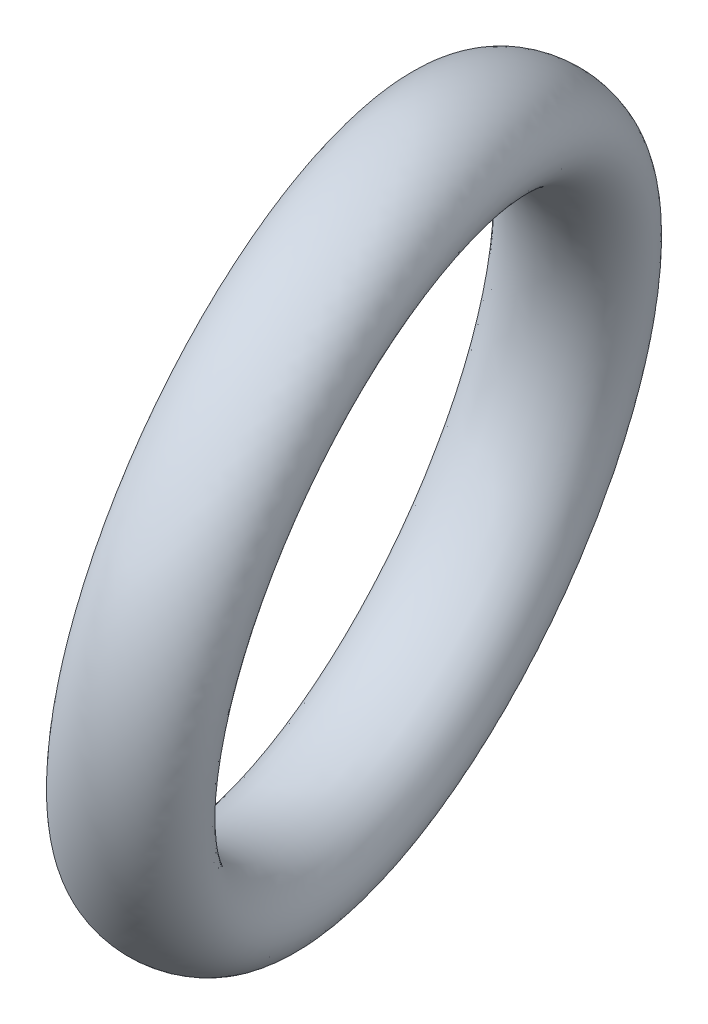
SolidWorks part; units mm, degrees
ref_plane "Front Plane" through (0, 0, 0) normal (0, 0, 1) x (1, 0, 0)
ref_plane "Top Plane" through (0, 0, 0) normal (0, 1, 0) x (1, 0, 0)
ref_plane "Right Plane" through (0, 0, 0) normal (1, 0, 0) x (0, 0, -1)
sketch "Sketch1" plane through (0, 0, 0) normal (1, 0, 0) x (0, 0, -1)
  line L0 (0, 0) -> (254, 439.9409) construction
  line L1 (0, 0) -> (0, 60.7436) construction
  line L2 (0, 0) -> (50.8, 0) construction
  line L3 (50.8, 0) -> (50.8, 263.525) construction
  line L4 (50.8, 263.525) -> (126.8097, 219.6408) construction
  circle A0 centre (50.8, 263.525) radius 263.525
  dimension "D3" = 527.05
  dimension "D1" = 508
  dimension "D2" = 30
  dimension "D4" = 50.8
  dimension "D5" = 87.7684
sketch "Sketch2" plane through (0, 0, 0) normal (0, 1, 0) x (1, 0, 0)
  line L0 (-22.2653, 83.0954) -> (0, 0) construction
  line L1 (0, 0) -> (262.9601, -981.3806) construction
  line L2 (0, 0) -> (0, 254) construction
  point P4 (-55.4206, 141.2482)
  point P7 (-22.2653, 83.0954)
  point P8 (0, 0)
  dimension "D1" = 1016
  dimension "D2" = 15
ref_plane "Plane1" through (0, 0, 0) normal (0.9553, -0.1478, -0.256) x (-0.253, 0.0391, -0.9667)
sketch "Sketch4" plane through (0, 0, 0) normal (0.9553, -0.1478, -0.256) x (-0.253, 0.0391, -0.9667)
  line L1 (247, 570.8078) -> (59.4203, 260.4271) construction
  line L2 (0, 0) -> (262.7542, 434.7692) construction
  circle A0 centre (59.4203, 260.4271) radius 263.525
  point P2 (0, 0)
  point P6 (167.2025, 261.5589)
  point P7 (133.4312, 274.9509)
  point P9 (0, 0)
  point P10 (0, 0)
  point P11 (59.4203, 260.4271)
  point P13 (59.4203, 260.4271)
  dimension "D1" = 527.05
ref_plane "Plane3" through (24.7832, 259.691, -57.4406) normal (0, -0.866, 0.5) x (-1, 0, 0)
sketch "Sketch6" plane through (24.7832, 259.691, -57.4406) normal (0, -0.866, 0.5) x (-1, 0, 0)
  line L0 (77.8919, 251.7504) -> (-77.8919, -251.7504) construction
  line L1 (77.8919, 251.7504) -> (-77.8919, -251.7504) construction
  line L2 (0, 0) -> (197.111, -60.9864) construction
  ellipse E0 centre (67.5467, 218.3143) end of major axis (22.169, 232.3542) minor radius 35
  ellipse E1 centre (67.5467, -218.3143) end of major axis (22.169, -232.3542) minor radius 35 construction
  dimension "D1" = 95
  dimension "D2" = 70
ref_plane "Plane4" through (0, 0, -57.4406) normal (0, 0, 1) x (1, 0, 0)
revolve "Revolve1" add sketch "Sketch6" angle 360 about L2
sketch "Sketch8" plane through (0, 0, -57.4406) normal (0, 0, 1) x (1, 0, 0)
  line L2 (-134.3553, 0) -> (355.2062, 0) construction
  line L10 (189.8207, 0) -> (-189.8207, 0) construction
  spline S0 degree 3 poles (38.5657, 27.377) (38.2434, 25.2939) (37.9153, 23.9442) (37.0485, 21.317) (36.5098, 20.0396) (35.5483, 18.1763) (35.2019, 17.564) (34.4707, 16.3761) (34.0847, 15.7978) (32.8691, 14.1074) (31.9819, 13.0395) (30.5457, 11.5186) (30.0476, 11.0237) (29.0274, 10.0696) (28.5053, 9.6102) (26.9053, 8.2807) (25.794, 7.4594) (23.4921, 5.9327) (22.3013, 5.2274) (19.8462, 3.9243) (18.5779, 3.3253) (14.7407, 1.7099) (12.1185, 0.86) (8.1038, -0.1266) (6.7518, -0.4069) (4.7042, -0.7576) (4.0183, -0.8628) (2.6401, -1.0501) (1.9471, -1.1323) (-1.5118, -1.484) (-4.2751, -1.5798) (-9.7946, -1.4301) (-12.5508, -1.1843) (-16.6796, -0.5583) (-18.0471, -0.3076) (-20.7501, 0.2741) (-22.0881, 0.6054) (-26.061, 1.7204) (-28.6557, 2.6243) (-32.4612, 4.237) (-33.7152, 4.8175) (-36.1923, 6.0706) (-37.4183, 6.7453) (-40.9905, 8.8857) (-43.2492, 10.4739) (-46.4278, 13.1311) (-47.4523, 14.063) (-48.9301, 15.538) (-49.414, 16.0439) (-50.3539, 17.0757) (-50.8097, 17.6012) (-52.1334, 19.2081) (-52.9578, 20.3193) (-54.4793, 22.6293) (-55.1764, 23.8281) (-56.1131, 25.7013) (-56.4075, 26.3396) (-56.9494, 27.6251) (-57.1981, 28.2742) (-57.8747, 30.241) (-58.2337, 31.5784) (-58.6205, 33.6276) (-58.7241, 34.3179) (-58.8769, 35.7139) (-58.9252, 36.4108) (-58.9856, 38.4928) (-58.9138, 39.8717) (-58.6355, 41.926) (-58.5142, 42.6084) (-58.2131, 43.9684) (-58.0322, 44.6494) (-57.4086, 46.6545) (-56.887, 47.9414) (-55.9572, 49.8027) (-55.6226, 50.4115) (-54.9052, 51.6065) (-54.5209, 52.1947) (-53.3075, 53.9103) (-52.4226, 54.9843) (-50.5188, 57.0087) (-49.4997, 57.9592) (-47.3381, 59.7459) (-46.2153, 60.5659) (-42.739, 62.8366) (-40.2782, 64.0999) (-37.0533, 65.4183) (-36.3996, 65.6692) (-35.0885, 66.1413) (-34.4301, 66.3631) (-32.4471, 66.9881) (-31.1144, 67.3509) (-27.0874, 68.2923) (-24.3642, 68.7251) (-20.917, 69.0469) (-20.2254, 69.1002) (-18.8378, 69.1849) (-18.1407, 69.2163) (-16.0532, 69.2778) (-14.666, 69.2752) (-10.5169, 69.1431) (-7.7675, 68.8899) (-3.6679, 68.2696) (-2.3055, 68.0225) (0.411, 67.4461) (1.7686, 67.1156) (5.7807, 66.0099) (8.3869, 65.1196) (13.4574, 63.0214) (15.9218, 61.814) (19.4973, 59.7318) (20.6688, 58.9924) (22.3921, 57.8072) (22.9614, 57.3989) (24.0777, 56.5632) (24.6259, 56.1349) (27.3157, 53.9399) (29.3058, 52.0147) (31.9913, 48.813) (32.8384, 47.6879) (34.3795, 45.3705) (35.0785, 44.1732) (36.3184, 41.6937) (36.8596, 40.4115) (37.7602, 37.7495) (38.1092, 36.3997) (38.5935, 33.6678) (38.7294, 32.2847) (38.7599, 30.1818) (38.7409, 29.4767) (38.6438, 28.0761) (38.5657, 27.377) (38.2434, 25.2939) (37.9153, 23.9442) knots -0.007812 -0.007812 0 0 0.015625 0.015625 0.03125 0.03125 0.039062 0.039062 0.046875 0.046875 0.0625 0.0625 0.070312 0.070312 0.078125 0.078125 0.09375 0.09375 0.109375 0.109375 0.125 0.125 0.15625 0.15625 0.171875 0.171875 0.179687 0.179687 0.1875 0.1875 0.21875 0.21875 0.25 0.25 0.265625 0.265625 0.28125 0.28125 0.3125 0.3125 0.328125 0.328125 0.34375 0.34375 0.375 0.375 0.390625 0.390625 0.398437 0.398437 0.40625 0.40625 0.421875 0.421875 0.4375 0.4375 0.445312 0.445312 0.453125 0.453125 0.46875 0.46875 0.476562 0.476562 0.484375 0.484375 0.5 0.5 0.507812 0.507812 0.515625 0.515625 0.53125 0.53125 0.539062 0.539062 0.546875 0.546875 0.5625 0.5625 0.578125 0.578125 0.59375 0.59375 0.625 0.625 0.632812 0.632812 0.640625 0.640625 0.65625 0.65625 0.6875 0.6875 0.695312 0.695312 0.703125 0.703125 0.71875 0.71875 0.75 0.75 0.765625 0.765625 0.78125 0.78125 0.8125 0.8125 0.84375 0.84375 0.859375 0.859375 0.867187 0.867187 0.875 0.875 0.90625 0.90625 0.921875 0.921875 0.9375 0.9375 0.953125 0.953125 0.96875 0.96875 0.984375 0.984375 0.992188 0.992188 1 1 1.015625 1.015625 1.03125 only from (38.4583, 26.6826) to (38.4583, 26.6826)
  spline S1 degree 3 poles (108.3345, 478.3699) (108.0121, 476.2854) (107.6835, 474.9346) (106.8127, 472.3061) (106.2703, 471.0285) (105.2989, 469.166) (104.9491, 468.5556) (104.2104, 467.3722) (103.8201, 466.7966) (102.5898, 465.1157) (101.6907, 464.0559) (100.2331, 462.5503) (99.7276, 462.0613) (98.6945, 461.1223) (98.1657, 460.6708) (96.5451, 459.3667) (95.4193, 458.564) (93.087, 457.0773) (91.8805, 456.3934) (90.0149, 455.4497) (89.3823, 455.1482) (88.1104, 454.577) (87.4703, 454.3067) (84.2495, 453.0264) (81.6097, 452.2286) (77.5707, 451.3165) (76.211, 451.0605) (73.4661, 450.6399) (72.0772, 450.4754) (67.9292, 450.1194) (65.1732, 450.0613) (59.6781, 450.2701) (56.9389, 450.5373) (52.8427, 451.1807) (51.4795, 451.4358) (48.7572, 452.0298) (47.4111, 452.366) (43.4217, 453.49) (40.8252, 454.3928) (35.765, 456.5217) (33.3011, 457.7472) (30.3173, 459.513) (29.7254, 459.8779) (28.5518, 460.6328) (27.9714, 461.022) (26.2608, 462.2186) (25.157, 463.0578) (21.963, 465.7085) (19.9881, 467.6507) (16.4315, 471.9806) (14.9086, 474.2971) (13.3934, 477.4218) (13.11, 478.0583) (12.5857, 479.3565) (12.3453, 480.0173) (11.7025, 482.0078) (11.3736, 483.3552) (11.0398, 485.4091) (10.9551, 486.0992) (10.8417, 487.4909) (10.8131, 488.1958) (10.8155, 490.294) (10.9328, 491.6755) (11.3936, 494.4046) (11.7378, 495.754) (12.6546, 498.4111) (13.2154, 499.6855) (14.5221, 502.1366) (15.2682, 503.3131) (16.936, 505.5733) (17.8388, 506.6318) (19.7633, 508.6238) (20.7851, 509.5574) (22.3989, 510.873) (22.9504, 511.2973) (24.0796, 512.1185) (24.6582, 512.5159) (27.5813, 514.4152) (30.0393, 515.6774) (33.8713, 517.2582) (35.1732, 517.7323) (37.1607, 518.3686) (37.8303, 518.5685) (39.1741, 518.942) (39.8475, 519.1154) (43.2215, 519.9187) (45.9429, 520.3594) (51.425, 520.8836) (54.1858, 520.9668) (57.6606, 520.8534) (58.3578, 520.8197) (59.7464, 520.7309) (60.4385, 520.6758) (62.5084, 520.479) (63.8796, 520.3059) (67.9679, 519.6627) (70.6596, 519.0701) (74.6451, 517.9288) (75.965, 517.5061) (77.931, 516.8057) (78.5849, 516.5608) (79.8798, 516.0515) (80.5216, 515.7868) (83.7021, 514.413) (86.156, 513.154) (89.6888, 511.0038) (90.8416, 510.2432) (92.5304, 509.0308) (93.0866, 508.6147) (94.1847, 507.7573) (94.7276, 507.3152) (97.382, 505.057) (99.3296, 503.0906) (101.9397, 499.8583) (102.7578, 498.7329) (104.2724, 496.3748) (104.9554, 495.1629) (106.1621, 492.6686) (106.6858, 491.3862) (107.3377, 489.4034) (107.5328, 488.7321) (107.8742, 487.37) (108.0187, 486.6867) (108.3726, 484.6301) (108.5025, 483.2502) (108.5293, 481.1662) (108.51, 480.4692) (108.4127, 479.0702) (108.3345, 478.3699) (108.0121, 476.2854) (107.6835, 474.9346) knots -0.007813 -0.007813 0 0 0.015625 0.015625 0.03125 0.03125 0.039062 0.039062 0.046875 0.046875 0.0625 0.0625 0.070312 0.070312 0.078125 0.078125 0.09375 0.09375 0.109375 0.109375 0.117187 0.117187 0.125 0.125 0.15625 0.15625 0.171875 0.171875 0.1875 0.1875 0.21875 0.21875 0.25 0.25 0.265625 0.265625 0.28125 0.28125 0.3125 0.3125 0.34375 0.34375 0.351562 0.351562 0.359375 0.359375 0.375 0.375 0.40625 0.40625 0.4375 0.4375 0.445312 0.445312 0.453125 0.453125 0.46875 0.46875 0.476562 0.476562 0.484375 0.484375 0.5 0.5 0.515625 0.515625 0.53125 0.53125 0.546875 0.546875 0.5625 0.5625 0.578125 0.578125 0.585937 0.585937 0.59375 0.59375 0.625 0.625 0.640625 0.640625 0.648437 0.648437 0.65625 0.65625 0.6875 0.6875 0.71875 0.71875 0.726562 0.726562 0.734375 0.734375 0.75 0.75 0.78125 0.78125 0.796875 0.796875 0.804687 0.804687 0.8125 0.8125 0.84375 0.84375 0.859375 0.859375 0.867187 0.867187 0.875 0.875 0.90625 0.90625 0.921875 0.921875 0.9375 0.9375 0.953125 0.953125 0.960937 0.960937 0.96875 0.96875 0.984375 0.984375 0.992187 0.992187 1 1 1.015625 1.015625 1.03125 only from (108.227, 477.6751) to (108.227, 477.6751)
  spline S2 degree 3 poles (108.3345, 478.3699) (108.0121, 476.2854) (107.6835, 474.9346) (106.8127, 472.3061) (106.2703, 471.0285) (105.2989, 469.166) (104.9491, 468.5556) (104.2104, 467.3722) (103.8201, 466.7966) (102.5898, 465.1157) (101.6907, 464.0559) (100.2331, 462.5503) (99.7276, 462.0613) (98.6945, 461.1223) (98.1657, 460.6708) (96.5451, 459.3667) (95.4193, 458.564) (93.087, 457.0773) (91.8805, 456.3934) (90.0149, 455.4497) (89.3823, 455.1482) (88.1104, 454.577) (87.4703, 454.3067) (84.2495, 453.0264) (81.6097, 452.2286) (77.5707, 451.3165) (76.211, 451.0605) (73.4661, 450.6399) (72.0772, 450.4754) (67.9292, 450.1194) (65.1732, 450.0613) (59.6781, 450.2701) (56.9389, 450.5373) (52.8427, 451.1807) (51.4795, 451.4358) (48.7572, 452.0298) (47.4111, 452.366) (43.4217, 453.49) (40.8252, 454.3928) (35.765, 456.5217) (33.3011, 457.7472) (30.3173, 459.513) (29.7254, 459.8779) (28.5518, 460.6328) (27.9714, 461.022) (26.2608, 462.2186) (25.157, 463.0578) (21.963, 465.7085) (19.9881, 467.6507) (16.4315, 471.9806) (14.9086, 474.2971) (13.3934, 477.4218) (13.11, 478.0583) (12.5857, 479.3565) (12.3453, 480.0173) (11.7025, 482.0078) (11.3736, 483.3552) (11.0398, 485.4091) (10.9551, 486.0992) (10.8417, 487.4909) (10.8131, 488.1958) (10.8155, 490.294) (10.9328, 491.6755) (11.3936, 494.4046) (11.7378, 495.754) (12.6546, 498.4111) (13.2154, 499.6855) (14.5221, 502.1366) (15.2682, 503.3131) (16.936, 505.5733) (17.8388, 506.6318) (19.7633, 508.6238) (20.7851, 509.5574) (22.3989, 510.873) (22.9504, 511.2973) (24.0796, 512.1185) (24.6582, 512.5159) (27.5813, 514.4152) (30.0393, 515.6774) (33.8713, 517.2582) (35.1732, 517.7323) (37.1607, 518.3686) (37.8303, 518.5685) (39.1741, 518.942) (39.8475, 519.1154) (43.2215, 519.9187) (45.9429, 520.3594) (51.425, 520.8836) (54.1858, 520.9668) (57.6606, 520.8534) (58.3578, 520.8197) (59.7464, 520.7309) (60.4385, 520.6758) (62.5084, 520.479) (63.8796, 520.3059) (67.9679, 519.6627) (70.6596, 519.0701) (74.6451, 517.9288) (75.965, 517.5061) (77.931, 516.8057) (78.5849, 516.5608) (79.8798, 516.0515) (80.5216, 515.7868) (83.7021, 514.413) (86.156, 513.154) (89.6888, 511.0038) (90.8416, 510.2432) (92.5304, 509.0308) (93.0866, 508.6147) (94.1847, 507.7573) (94.7276, 507.3152) (97.382, 505.057) (99.3296, 503.0906) (101.9397, 499.8583) (102.7578, 498.7329) (104.2724, 496.3748) (104.9554, 495.1629) (106.1621, 492.6686) (106.6858, 491.3862) (107.3377, 489.4034) (107.5328, 488.7321) (107.8742, 487.37) (108.0187, 486.6867) (108.3726, 484.6301) (108.5025, 483.2502) (108.5293, 481.1662) (108.51, 480.4692) (108.4127, 479.0702) (108.3345, 478.3699) (108.0121, 476.2854) (107.6835, 474.9346) knots -0.007813 -0.007813 0 0 0.015625 0.015625 0.03125 0.03125 0.039062 0.039062 0.046875 0.046875 0.0625 0.0625 0.070312 0.070312 0.078125 0.078125 0.09375 0.09375 0.109375 0.109375 0.117187 0.117187 0.125 0.125 0.15625 0.15625 0.171875 0.171875 0.1875 0.1875 0.21875 0.21875 0.25 0.25 0.265625 0.265625 0.28125 0.28125 0.3125 0.3125 0.34375 0.34375 0.351562 0.351562 0.359375 0.359375 0.375 0.375 0.40625 0.40625 0.4375 0.4375 0.445312 0.445312 0.453125 0.453125 0.46875 0.46875 0.476562 0.476562 0.484375 0.484375 0.5 0.5 0.515625 0.515625 0.53125 0.53125 0.546875 0.546875 0.5625 0.5625 0.578125 0.578125 0.585937 0.585937 0.59375 0.59375 0.625 0.625 0.640625 0.640625 0.648437 0.648437 0.65625 0.65625 0.6875 0.6875 0.71875 0.71875 0.726562 0.726562 0.734375 0.734375 0.75 0.75 0.78125 0.78125 0.796875 0.796875 0.804687 0.804687 0.8125 0.8125 0.84375 0.84375 0.859375 0.859375 0.867187 0.867187 0.875 0.875 0.90625 0.90625 0.921875 0.921875 0.9375 0.9375 0.953125 0.953125 0.960937 0.960937 0.96875 0.96875 0.984375 0.984375 0.992187 0.992187 1 1 1.015625 1.015625 1.03125 only from (108.227, 477.6751) to (108.227, 477.6751)
  spline S3 degree 3 poles (38.5657, 27.377) (38.2434, 25.2939) (37.9153, 23.9442) (37.0485, 21.317) (36.5098, 20.0396) (35.5483, 18.1763) (35.2019, 17.564) (34.4707, 16.3761) (34.0847, 15.7978) (32.8691, 14.1074) (31.9819, 13.0395) (30.5457, 11.5186) (30.0476, 11.0237) (29.0274, 10.0696) (28.5053, 9.6102) (26.9053, 8.2807) (25.794, 7.4594) (23.4921, 5.9327) (22.3013, 5.2274) (19.8462, 3.9243) (18.5779, 3.3253) (14.7407, 1.7099) (12.1185, 0.86) (8.1038, -0.1266) (6.7518, -0.4069) (4.7042, -0.7576) (4.0183, -0.8628) (2.6401, -1.0501) (1.9471, -1.1323) (-1.5118, -1.484) (-4.2751, -1.5798) (-9.7946, -1.4301) (-12.5508, -1.1843) (-16.6796, -0.5583) (-18.0471, -0.3076) (-20.7501, 0.2741) (-22.0881, 0.6054) (-26.061, 1.7204) (-28.6557, 2.6243) (-32.4612, 4.237) (-33.7152, 4.8175) (-36.1923, 6.0706) (-37.4183, 6.7453) (-40.9905, 8.8857) (-43.2492, 10.4739) (-46.4278, 13.1311) (-47.4523, 14.063) (-48.9301, 15.538) (-49.414, 16.0439) (-50.3539, 17.0757) (-50.8097, 17.6012) (-52.1334, 19.2081) (-52.9578, 20.3193) (-54.4793, 22.6293) (-55.1764, 23.8281) (-56.1131, 25.7013) (-56.4075, 26.3396) (-56.9494, 27.6251) (-57.1981, 28.2742) (-57.8747, 30.241) (-58.2337, 31.5784) (-58.6205, 33.6276) (-58.7241, 34.3179) (-58.8769, 35.7139) (-58.9252, 36.4108) (-58.9856, 38.4928) (-58.9138, 39.8717) (-58.6355, 41.926) (-58.5142, 42.6084) (-58.2131, 43.9684) (-58.0322, 44.6494) (-57.4086, 46.6545) (-56.887, 47.9414) (-55.9572, 49.8027) (-55.6226, 50.4115) (-54.9052, 51.6065) (-54.5209, 52.1947) (-53.3075, 53.9103) (-52.4226, 54.9843) (-50.5188, 57.0087) (-49.4997, 57.9592) (-47.3381, 59.7459) (-46.2153, 60.5659) (-42.739, 62.8366) (-40.2782, 64.0999) (-37.0533, 65.4183) (-36.3996, 65.6692) (-35.0885, 66.1413) (-34.4301, 66.3631) (-32.4471, 66.9881) (-31.1144, 67.3509) (-27.0874, 68.2923) (-24.3642, 68.7251) (-20.917, 69.0469) (-20.2254, 69.1002) (-18.8378, 69.1849) (-18.1407, 69.2163) (-16.0532, 69.2778) (-14.666, 69.2752) (-10.5169, 69.1431) (-7.7675, 68.8899) (-3.6679, 68.2696) (-2.3055, 68.0225) (0.411, 67.4461) (1.7686, 67.1156) (5.7807, 66.0099) (8.3869, 65.1196) (13.4574, 63.0214) (15.9218, 61.814) (19.4973, 59.7318) (20.6688, 58.9924) (22.3921, 57.8072) (22.9614, 57.3989) (24.0777, 56.5632) (24.6259, 56.1349) (27.3157, 53.9399) (29.3058, 52.0147) (31.9913, 48.813) (32.8384, 47.6879) (34.3795, 45.3705) (35.0785, 44.1732) (36.3184, 41.6937) (36.8596, 40.4115) (37.7602, 37.7495) (38.1092, 36.3997) (38.5935, 33.6678) (38.7294, 32.2847) (38.7599, 30.1818) (38.7409, 29.4767) (38.6438, 28.0761) (38.5657, 27.377) (38.2434, 25.2939) (37.9153, 23.9442) knots -0.007812 -0.007812 0 0 0.015625 0.015625 0.03125 0.03125 0.039062 0.039062 0.046875 0.046875 0.0625 0.0625 0.070312 0.070312 0.078125 0.078125 0.09375 0.09375 0.109375 0.109375 0.125 0.125 0.15625 0.15625 0.171875 0.171875 0.179687 0.179687 0.1875 0.1875 0.21875 0.21875 0.25 0.25 0.265625 0.265625 0.28125 0.28125 0.3125 0.3125 0.328125 0.328125 0.34375 0.34375 0.375 0.375 0.390625 0.390625 0.398437 0.398437 0.40625 0.40625 0.421875 0.421875 0.4375 0.4375 0.445312 0.445312 0.453125 0.453125 0.46875 0.46875 0.476562 0.476562 0.484375 0.484375 0.5 0.5 0.507812 0.507812 0.515625 0.515625 0.53125 0.53125 0.539062 0.539062 0.546875 0.546875 0.5625 0.5625 0.578125 0.578125 0.59375 0.59375 0.625 0.625 0.632812 0.632812 0.640625 0.640625 0.65625 0.65625 0.6875 0.6875 0.695312 0.695312 0.703125 0.703125 0.71875 0.71875 0.75 0.75 0.765625 0.765625 0.78125 0.78125 0.8125 0.8125 0.84375 0.84375 0.859375 0.859375 0.867187 0.867187 0.875 0.875 0.90625 0.90625 0.921875 0.921875 0.9375 0.9375 0.953125 0.953125 0.96875 0.96875 0.984375 0.984375 0.992188 0.992188 1 1 1.015625 1.015625 1.03125 only from (38.4583, 26.6826) to (38.4583, 26.6826)
sketch "Sketch9" plane through (0, 0, 0) normal (1, 0, 0) x (0, 0, -1)
  line L0 (-50.0794, 27.7046) -> (197.8955, 27.7046)
  line L1 (0, 0) -> (254, 439.9409) construction
  line L2 (15.9952, 27.7046) -> (126.8097, 219.6408)
  line L3 (-115.2994, 359.4225) -> (230.1807, 159.9595) construction
  spline S1 degree 3 poles (239.2015, 154.581) (243.9964, 162.886) (247.7851, 171.4112) (252.2369, 184.6585) (253.516, 189.1507) (254.8733, 194.8561) (255.1327, 196.0017) (255.6275, 198.3018) (255.8631, 199.4572) (256.5317, 202.9211) (256.9274, 205.232) (257.9727, 212.169) (258.4811, 216.7995) (259.153, 226.0713) (259.3164, 230.7125) (259.3181, 240.0051) (259.1563, 244.6564) (258.6779, 251.6407) (258.4791, 253.97) (258.1224, 257.4658) (257.9938, 258.6314) (257.717, 260.9631) (257.5689, 262.1298) (256.1527, 272.5996) (254.3041, 281.7444) (249.5272, 299.7376) (246.5977, 308.5858) (242.2805, 319.4664) (241.3836, 321.6348) (239.5265, 325.9479) (238.569, 328.0865) (235.6116, 334.4495) (233.5269, 338.6213) (226.9466, 350.9341) (222.1253, 358.8729) (211.6594, 374.2392) (206.0142, 381.6663) (193.9283, 396.0266) (187.5592, 402.8738) (174.2413, 415.9699) (167.2903, 422.2177) (156.4984, 431.2136) (152.8403, 434.1498) (145.4444, 439.9037) (141.7035, 442.7234) (134.1657, 448.2879) (130.3681, 451.0319) (124.669, 455.1443) (122.7691, 456.5148) (118.9805, 459.2707) (117.0918, 460.6558) (113.3449, 463.4643) (111.4863, 464.8873) (107.8322, 467.8124) (106.0355, 469.313) (103.4375, 471.686) (102.5869, 472.4991) (100.9489, 474.1742) (100.1601, 475.0369) (98.6765, 476.8411) (97.9806, 477.7815) (97.0576, 479.2932) (96.7717, 479.8127) (96.2665, 480.8771) (96.0459, 481.4237) (95.6916, 482.5559) (95.5621, 483.1299) (95.4565, 484.0003) (95.436, 484.2922) (95.428, 484.8801) (95.4406, 485.1781) (95.5321, 486.0636) (95.6625, 486.634) (95.9573, 487.4612) (96.0721, 487.7322) (96.3341, 488.2648) (96.4803, 488.5241) (96.9525, 489.2707) (97.3145, 489.7327) (97.9136, 490.3831) (98.1235, 490.5935) (98.5559, 490.9973) (98.7781, 491.1905) (99.9147, 492.1196) (100.9039, 492.747) (102.463, 493.5789) (102.9946, 493.8367) (104.0655, 494.315) (104.6066, 494.5364) (106.2439, 495.1569) (107.3542, 495.5123) (109.6024, 496.1364) (110.7406, 496.4046) (113.0396, 496.8703) (114.196, 497.0666) (117.6604, 497.5618) (119.9736, 497.7703) (124.6056, 498.0047) (126.9243, 498.0299) (131.5664, 497.9267) (133.8898, 497.7982) (137.3779, 497.503) (138.5412, 497.3874) (140.8559, 497.1251) (142.0091, 496.9783) (147.7552, 496.1701) (152.2892, 495.2891) (161.2506, 493.1287) (165.6776, 491.8482) (174.4334, 488.9205) (178.7621, 487.2729) (184.1138, 484.9926) (185.1812, 484.5254) (187.3015, 483.573) (188.3554, 483.0874) (191.499, 481.6026) (193.5704, 480.5757) (199.7143, 477.3876) (203.7167, 475.1192) (211.5431, 470.3105) (215.3671, 467.7699) (222.8414, 462.4236) (226.4916, 459.6177) (231.8373, 455.211) (233.5976, 453.7091) (237.0748, 450.6391) (238.7944, 449.0682) (247.2306, 441.0973) (253.4898, 434.3305) (265.0814, 420.0587) (270.4134, 412.5535) (276.4969, 402.7087) (277.6844, 400.7165) (280.0005, 396.6852) (281.1244, 394.6541) (284.3898, 388.5252) (286.4278, 384.3874) (292.1351, 371.8224) (295.3996, 363.2443) (299.4979, 350.0794) (300.7305, 345.6413) (302.3772, 338.9089) (302.8924, 336.6521) (303.8547, 332.1133) (304.3021, 329.8294) (306.3543, 318.4217) (307.4206, 309.2765) (308.4564, 290.9502) (308.4255, 281.7689) (307.5672, 267.9703) (307.1455, 263.3663) (306.3092, 256.4536) (305.9967, 254.1513) (305.3084, 249.571) (304.9322, 247.2899) (302.8946, 235.9291) (300.7638, 226.9828) (295.5932, 209.3486) (292.5522, 200.661) (288.2552, 189.9425) (287.3711, 187.8058) (285.556, 183.5457) (284.6243, 181.4212) (281.7747, 175.0924) (279.7985, 170.9246) (275.7161, 162.6762) (273.61, 158.5955) (269.2859, 150.5094) (267.068, 146.5038) (262.5293, 138.5619) (260.2084, 134.6255) (255.4602, 126.8242) (253.0326, 122.9594) (245.5694, 111.4864) (240.3528, 103.9997) (229.2814, 89.4548) (223.4253, 82.3975) (214.0526, 72.2068) (210.8304, 68.8756) (205.8378, 63.986) (204.1443, 62.3715) (200.7237, 59.1995) (198.9951, 57.6403) (190.2603, 49.9797) (182.9781, 44.2833) (167.8083, 33.7791) (159.9212, 28.9706) (149.6662, 23.5417) (147.5953, 22.485) (143.4132, 20.431) (141.2996, 19.4326) (134.913, 16.5354) (130.6185, 14.745) (117.627, 9.7897) (108.822, 7.0393) (90.9255, 2.6403) (81.834, 0.9914) (70.283, -0.3527) (67.9635, -0.5855) (64.4698, -0.8798) (63.3023, -0.9687) (60.971, -1.1276) (59.8063, -1.1976) (53.9872, -1.5008) (49.3466, -1.5935) (35.4682, -1.4293) (26.2735, -0.7319) (8.0003, 1.8495) (-1.0782, 3.7329) (-12.3487, 6.8798) (-14.5896, 7.5465) (-19.0321, 8.9503) (-21.2358, 9.6879) (-27.7946, 12.0076) (-32.0974, 13.6962) (-44.7959, 19.1901) (-52.9834, 23.4198) (-64.8181, 30.675) (-68.6882, 33.2459) (-74.3727, 37.3484) (-76.2506, 38.7598) (-79.9351, 41.6457) (-81.7444, 43.1219) (-87.0713, 47.6527) (-90.4885, 50.8088) (-97.0335, 57.4134) (-100.1618, 60.8614) (-103.864, 65.3819) (-104.5939, 66.2966) (-106.0316, 68.1484) (-106.7402, 69.0865) (-108.8242, 71.9276) (-110.1571, 73.8556) (-112.6972, 77.7873) (-113.9045, 79.7909) (-116.1712, 83.8871) (-117.2314, 85.9799) (-119.162, 90.2769) (-120.0253, 92.4621) (-120.9253, 95.258) (-121.0961, 95.8205) (-121.4172, 96.9529) (-121.5678, 97.5238) (-121.9817, 99.2395) (-122.2084, 100.3877) (-122.5322, 102.6962) (-122.6303, 103.8563) (-122.6344, 105.6095) (-122.6117, 106.1961) (-122.503, 107.3752) (-122.4161, 107.97) (-122.1636, 109.1316) (-121.9982, 109.702) (-121.6726, 110.537) (-121.551, 110.8115) (-121.2839, 111.3413) (-121.1379, 111.598) (-120.8188, 112.0938) (-120.6458, 112.3328) (-120.2703, 112.7917) (-120.0663, 113.013) (-119.4179, 113.6342) (-118.9432, 113.9871) (-118.1733, 114.4329) (-117.9059, 114.568) (-117.3574, 114.8093) (-117.0791, 114.9145) (-116.2338, 115.1901) (-115.6564, 115.3207) (-114.7742, 115.4555) (-114.4765, 115.4902) (-113.8828, 115.5408) (-113.5865, 115.557) (-112.6987, 115.5818) (-112.1085, 115.5672) (-110.9306, 115.4914) (-110.343, 115.4301) (-109.1696, 115.2712) (-108.5825, 115.1733) (-106.8353, 114.8383) (-105.6894, 114.5614) (-103.4212, 113.9407) (-102.299, 113.5964) (-100.0707, 112.8624) (-98.9645, 112.4725) (-95.6629, 111.2554) (-93.4838, 110.3817) (-89.1465, 108.5744) (-86.9887, 107.6399) (-82.6826, 105.7449) (-80.5345, 104.7842) (-74.0928, 101.8944) (-69.8014, 99.9597) (-61.1889, 96.1705) (-56.8683, 94.3147) (-48.1793, 90.732) (-43.8111, 89.0047) (-30.6179, 84.0616) (-21.7038, 81.0865) (-8.1122, 77.2188) (-3.5451, 76.028) (5.6675, 73.8585) (10.2818, 72.8872) (24.1429, 70.3225) (33.4108, 69.0778) (52.0032, 67.5593) (61.3277, 67.2849) (75.3595, 67.6459) (80.0443, 67.8953) (87.0832, 68.4712) (89.4315, 68.6969) (94.1321, 69.2172) (96.4877, 69.5124) (108.2045, 71.1552) (117.4204, 73.0033) (135.5315, 77.7868) (144.427, 80.7212) (157.5119, 85.9992) (161.8303, 87.9051) (167.1705, 90.4831) (168.236, 91.0087) (170.3532, 92.0759) (171.4059, 92.6179) (174.5463, 94.2693) (176.6162, 95.4042) (182.7538, 98.9119) (186.7497, 101.3876) (194.5407, 106.6266) (198.3358, 109.3898) (205.7095, 115.2262) (209.2881, 118.2993) (214.4755, 123.1674) (216.1778, 124.8368) (219.4908, 128.2392) (221.1041, 129.9741) (225.8103, 135.2828) (228.7697, 138.9605) (232.9257, 144.6976) (234.2638, 146.6468) (236.1982, 149.6271) (237.1471, 151.1315) (238.222, 152.9117) (238.7514, 153.8081) (238.9765, 154.1936) (239.1262, 154.451) (239.2015, 154.581) (243.9964, 162.886) (247.7851, 171.4112) knots -0.000244 -0.000244 0 0 0.015625 0.015625 0.023438 0.023438 0.025391 0.025391 0.027344 0.027344 0.03125 0.03125 0.039063 0.039063 0.046875 0.046875 0.054688 0.054688 0.058594 0.058594 0.060547 0.060547 0.0625 0.0625 0.078125 0.078125 0.09375 0.09375 0.097656 0.097656 0.101563 0.101563 0.109375 0.109375 0.125 0.125 0.140625 0.140625 0.15625 0.15625 0.171875 0.171875 0.179688 0.179688 0.1875 0.1875 0.195313 0.195313 0.199219 0.199219 0.203125 0.203125 0.207031 0.207031 0.210938 0.210938 0.212891 0.212891 0.214844 0.214844 0.216797 0.216797 0.217773 0.217773 0.21875 0.21875 0.219727 0.219727 0.220215 0.220215 0.220703 0.220703 0.22168 0.22168 0.222168 0.222168 0.222656 0.222656 0.223633 0.223633 0.224121 0.224121 0.224609 0.224609 0.226563 0.226563 0.227539 0.227539 0.228516 0.228516 0.230469 0.230469 0.232422 0.232422 0.234375 0.234375 0.238281 0.238281 0.242188 0.242188 0.246094 0.246094 0.248047 0.248047 0.25 0.25 0.257813 0.257813 0.265625 0.265625 0.273437 0.273437 0.275391 0.275391 0.277344 0.277344 0.28125 0.28125 0.289062 0.289062 0.296875 0.296875 0.304687 0.304687 0.308594 0.308594 0.3125 0.3125 0.328125 0.328125 0.34375 0.34375 0.347656 0.347656 0.351562 0.351562 0.359375 0.359375 0.375 0.375 0.382812 0.382812 0.386719 0.386719 0.390625 0.390625 0.40625 0.40625 0.421875 0.421875 0.429687 0.429687 0.433594 0.433594 0.4375 0.4375 0.453125 0.453125 0.46875 0.46875 0.472656 0.472656 0.476562 0.476562 0.484375 0.484375 0.492187 0.492187 0.5 0.5 0.507812 0.507812 0.515625 0.515625 0.53125 0.53125 0.546875 0.546875 0.554687 0.554687 0.558594 0.558594 0.5625 0.5625 0.578125 0.578125 0.59375 0.59375 0.597656 0.597656 0.601562 0.601562 0.609375 0.609375 0.625 0.625 0.640625 0.640625 0.644531 0.644531 0.646484 0.646484 0.648437 0.648437 0.65625 0.65625 0.671875 0.671875 0.6875 0.6875 0.691406 0.691406 0.695312 0.695312 0.703125 0.703125 0.71875 0.71875 0.726562 0.726562 0.730469 0.730469 0.734375 0.734375 0.742187 0.742187 0.75 0.75 0.751953 0.751953 0.753906 0.753906 0.757812 0.757812 0.761719 0.761719 0.765625 0.765625 0.769531 0.769531 0.770508 0.770508 0.771484 0.771484 0.773437 0.773437 0.775391 0.775391 0.776367 0.776367 0.777344 0.777344 0.77832 0.77832 0.778809 0.778809 0.779297 0.779297 0.779785 0.779785 0.780273 0.780273 0.78125 0.78125 0.781738 0.781738 0.782227 0.782227 0.783203 0.783203 0.783691 0.783691 0.78418 0.78418 0.785156 0.785156 0.786133 0.786133 0.787109 0.787109 0.789062 0.789062 0.791016 0.791016 0.792969 0.792969 0.796875 0.796875 0.800781 0.800781 0.804687 0.804687 0.8125 0.8125 0.820312 0.820312 0.828125 0.828125 0.84375 0.84375 0.851562 0.851562 0.859375 0.859375 0.875 0.875 0.890625 0.890625 0.898437 0.898437 0.902344 0.902344 0.90625 0.90625 0.921875 0.921875 0.9375 0.9375 0.945312 0.945312 0.947266 0.947266 0.949219 0.949219 0.953125 0.953125 0.960937 0.960937 0.96875 0.96875 0.976562 0.976562 0.980469 0.980469 0.984375 0.984375 0.992187 0.992187 0.996094 0.996094 0.998047 0.999023 0.999512 0.999756 0.999756 1 1 1.015625 1.015625 1.023438 only from (239.2753, 154.7087) to (239.2753, 154.7087)
  spline S2 degree 3 poles (239.2015, 154.581) (243.9964, 162.886) (247.7851, 171.4112) (252.2369, 184.6585) (253.516, 189.1507) (254.8733, 194.8561) (255.1327, 196.0017) (255.6275, 198.3018) (255.8631, 199.4572) (256.5317, 202.9211) (256.9274, 205.232) (257.9727, 212.169) (258.4811, 216.7995) (259.153, 226.0713) (259.3164, 230.7125) (259.3181, 240.0051) (259.1563, 244.6564) (258.6779, 251.6407) (258.4791, 253.97) (258.1224, 257.4658) (257.9938, 258.6314) (257.717, 260.9631) (257.5689, 262.1298) (256.1527, 272.5996) (254.3041, 281.7444) (249.5272, 299.7376) (246.5977, 308.5858) (242.2805, 319.4664) (241.3836, 321.6348) (239.5265, 325.9479) (238.569, 328.0865) (235.6116, 334.4495) (233.5269, 338.6213) (226.9466, 350.9341) (222.1253, 358.8729) (211.6594, 374.2392) (206.0142, 381.6663) (193.9283, 396.0266) (187.5592, 402.8738) (174.2413, 415.9699) (167.2903, 422.2177) (156.4984, 431.2136) (152.8403, 434.1498) (145.4444, 439.9037) (141.7035, 442.7234) (134.1657, 448.2879) (130.3681, 451.0319) (124.669, 455.1443) (122.7691, 456.5148) (118.9805, 459.2707) (117.0918, 460.6558) (113.3449, 463.4643) (111.4863, 464.8873) (107.8322, 467.8124) (106.0355, 469.313) (103.4375, 471.686) (102.5869, 472.4991) (100.9489, 474.1742) (100.1601, 475.0369) (98.6765, 476.8411) (97.9806, 477.7815) (97.0576, 479.2932) (96.7717, 479.8127) (96.2665, 480.8771) (96.0459, 481.4237) (95.6916, 482.5559) (95.5621, 483.1299) (95.4565, 484.0003) (95.436, 484.2922) (95.428, 484.8801) (95.4406, 485.1781) (95.5321, 486.0636) (95.6625, 486.634) (95.9573, 487.4612) (96.0721, 487.7322) (96.3341, 488.2648) (96.4803, 488.5241) (96.9525, 489.2707) (97.3145, 489.7327) (97.9136, 490.3831) (98.1235, 490.5935) (98.5559, 490.9973) (98.7781, 491.1905) (99.9147, 492.1196) (100.9039, 492.747) (102.463, 493.5789) (102.9946, 493.8367) (104.0655, 494.315) (104.6066, 494.5364) (106.2439, 495.1569) (107.3542, 495.5123) (109.6024, 496.1364) (110.7406, 496.4046) (113.0396, 496.8703) (114.196, 497.0666) (117.6604, 497.5618) (119.9736, 497.7703) (124.6056, 498.0047) (126.9243, 498.0299) (131.5664, 497.9267) (133.8898, 497.7982) (137.3779, 497.503) (138.5412, 497.3874) (140.8559, 497.1251) (142.0091, 496.9783) (147.7552, 496.1701) (152.2892, 495.2891) (161.2506, 493.1287) (165.6776, 491.8482) (174.4334, 488.9205) (178.7621, 487.2729) (184.1138, 484.9926) (185.1812, 484.5254) (187.3015, 483.573) (188.3554, 483.0874) (191.499, 481.6026) (193.5704, 480.5757) (199.7143, 477.3876) (203.7167, 475.1192) (211.5431, 470.3105) (215.3671, 467.7699) (222.8414, 462.4236) (226.4916, 459.6177) (231.8373, 455.211) (233.5976, 453.7091) (237.0748, 450.6391) (238.7944, 449.0682) (247.2306, 441.0973) (253.4898, 434.3305) (265.0814, 420.0587) (270.4134, 412.5535) (276.4969, 402.7087) (277.6844, 400.7165) (280.0005, 396.6852) (281.1244, 394.6541) (284.3898, 388.5252) (286.4278, 384.3874) (292.1351, 371.8224) (295.3996, 363.2443) (299.4979, 350.0794) (300.7305, 345.6413) (302.3772, 338.9089) (302.8924, 336.6521) (303.8547, 332.1133) (304.3021, 329.8294) (306.3543, 318.4217) (307.4206, 309.2765) (308.4564, 290.9502) (308.4255, 281.7689) (307.5672, 267.9703) (307.1455, 263.3663) (306.3092, 256.4536) (305.9967, 254.1513) (305.3084, 249.571) (304.9322, 247.2899) (302.8946, 235.9291) (300.7638, 226.9828) (295.5932, 209.3486) (292.5522, 200.661) (288.2552, 189.9425) (287.3711, 187.8058) (285.556, 183.5457) (284.6243, 181.4212) (281.7747, 175.0924) (279.7985, 170.9246) (275.7161, 162.6762) (273.61, 158.5955) (269.2859, 150.5094) (267.068, 146.5038) (262.5293, 138.5619) (260.2084, 134.6255) (255.4602, 126.8242) (253.0326, 122.9594) (245.5694, 111.4864) (240.3528, 103.9997) (229.2814, 89.4548) (223.4253, 82.3975) (214.0526, 72.2068) (210.8304, 68.8756) (205.8378, 63.986) (204.1443, 62.3715) (200.7237, 59.1995) (198.9951, 57.6403) (190.2603, 49.9797) (182.9781, 44.2833) (167.8083, 33.7791) (159.9212, 28.9706) (149.6662, 23.5417) (147.5953, 22.485) (143.4132, 20.431) (141.2996, 19.4326) (134.913, 16.5354) (130.6185, 14.745) (117.627, 9.7897) (108.822, 7.0393) (90.9255, 2.6403) (81.834, 0.9914) (70.283, -0.3527) (67.9635, -0.5855) (64.4698, -0.8798) (63.3023, -0.9687) (60.971, -1.1276) (59.8063, -1.1976) (53.9872, -1.5008) (49.3466, -1.5935) (35.4682, -1.4293) (26.2735, -0.7319) (8.0003, 1.8495) (-1.0782, 3.7329) (-12.3487, 6.8798) (-14.5896, 7.5465) (-19.0321, 8.9503) (-21.2358, 9.6879) (-27.7946, 12.0076) (-32.0974, 13.6962) (-44.7959, 19.1901) (-52.9834, 23.4198) (-64.8181, 30.675) (-68.6882, 33.2459) (-74.3727, 37.3484) (-76.2506, 38.7598) (-79.9351, 41.6457) (-81.7444, 43.1219) (-87.0713, 47.6527) (-90.4885, 50.8088) (-97.0335, 57.4134) (-100.1618, 60.8614) (-103.864, 65.3819) (-104.5939, 66.2966) (-106.0316, 68.1484) (-106.7402, 69.0865) (-108.8242, 71.9276) (-110.1571, 73.8556) (-112.6972, 77.7873) (-113.9045, 79.7909) (-116.1712, 83.8871) (-117.2314, 85.9799) (-119.162, 90.2769) (-120.0253, 92.4621) (-120.9253, 95.258) (-121.0961, 95.8205) (-121.4172, 96.9529) (-121.5678, 97.5238) (-121.9817, 99.2395) (-122.2084, 100.3877) (-122.5322, 102.6962) (-122.6303, 103.8563) (-122.6344, 105.6095) (-122.6117, 106.1961) (-122.503, 107.3752) (-122.4161, 107.97) (-122.1636, 109.1316) (-121.9982, 109.702) (-121.6726, 110.537) (-121.551, 110.8115) (-121.2839, 111.3413) (-121.1379, 111.598) (-120.8188, 112.0938) (-120.6458, 112.3328) (-120.2703, 112.7917) (-120.0663, 113.013) (-119.4179, 113.6342) (-118.9432, 113.9871) (-118.1733, 114.4329) (-117.9059, 114.568) (-117.3574, 114.8093) (-117.0791, 114.9145) (-116.2338, 115.1901) (-115.6564, 115.3207) (-114.7742, 115.4555) (-114.4765, 115.4902) (-113.8828, 115.5408) (-113.5865, 115.557) (-112.6987, 115.5818) (-112.1085, 115.5672) (-110.9306, 115.4914) (-110.343, 115.4301) (-109.1696, 115.2712) (-108.5825, 115.1733) (-106.8353, 114.8383) (-105.6894, 114.5614) (-103.4212, 113.9407) (-102.299, 113.5964) (-100.0707, 112.8624) (-98.9645, 112.4725) (-95.6629, 111.2554) (-93.4838, 110.3817) (-89.1465, 108.5744) (-86.9887, 107.6399) (-82.6826, 105.7449) (-80.5345, 104.7842) (-74.0928, 101.8944) (-69.8014, 99.9597) (-61.1889, 96.1705) (-56.8683, 94.3147) (-48.1793, 90.732) (-43.8111, 89.0047) (-30.6179, 84.0616) (-21.7038, 81.0865) (-8.1122, 77.2188) (-3.5451, 76.028) (5.6675, 73.8585) (10.2818, 72.8872) (24.1429, 70.3225) (33.4108, 69.0778) (52.0032, 67.5593) (61.3277, 67.2849) (75.3595, 67.6459) (80.0443, 67.8953) (87.0832, 68.4712) (89.4315, 68.6969) (94.1321, 69.2172) (96.4877, 69.5124) (108.2045, 71.1552) (117.4204, 73.0033) (135.5315, 77.7868) (144.427, 80.7212) (157.5119, 85.9992) (161.8303, 87.9051) (167.1705, 90.4831) (168.236, 91.0087) (170.3532, 92.0759) (171.4059, 92.6179) (174.5463, 94.2693) (176.6162, 95.4042) (182.7538, 98.9119) (186.7497, 101.3876) (194.5407, 106.6266) (198.3358, 109.3898) (205.7095, 115.2262) (209.2881, 118.2993) (214.4755, 123.1674) (216.1778, 124.8368) (219.4908, 128.2392) (221.1041, 129.9741) (225.8103, 135.2828) (228.7697, 138.9605) (232.9257, 144.6976) (234.2638, 146.6468) (236.1982, 149.6271) (237.1471, 151.1315) (238.222, 152.9117) (238.7514, 153.8081) (238.9765, 154.1936) (239.1262, 154.451) (239.2015, 154.581) (243.9964, 162.886) (247.7851, 171.4112) knots -0.000244 -0.000244 0 0 0.015625 0.015625 0.023438 0.023438 0.025391 0.025391 0.027344 0.027344 0.03125 0.03125 0.039063 0.039063 0.046875 0.046875 0.054688 0.054688 0.058594 0.058594 0.060547 0.060547 0.0625 0.0625 0.078125 0.078125 0.09375 0.09375 0.097656 0.097656 0.101563 0.101563 0.109375 0.109375 0.125 0.125 0.140625 0.140625 0.15625 0.15625 0.171875 0.171875 0.179688 0.179688 0.1875 0.1875 0.195313 0.195313 0.199219 0.199219 0.203125 0.203125 0.207031 0.207031 0.210938 0.210938 0.212891 0.212891 0.214844 0.214844 0.216797 0.216797 0.217773 0.217773 0.21875 0.21875 0.219727 0.219727 0.220215 0.220215 0.220703 0.220703 0.22168 0.22168 0.222168 0.222168 0.222656 0.222656 0.223633 0.223633 0.224121 0.224121 0.224609 0.224609 0.226563 0.226563 0.227539 0.227539 0.228516 0.228516 0.230469 0.230469 0.232422 0.232422 0.234375 0.234375 0.238281 0.238281 0.242188 0.242188 0.246094 0.246094 0.248047 0.248047 0.25 0.25 0.257813 0.257813 0.265625 0.265625 0.273437 0.273437 0.275391 0.275391 0.277344 0.277344 0.28125 0.28125 0.289062 0.289062 0.296875 0.296875 0.304687 0.304687 0.308594 0.308594 0.3125 0.3125 0.328125 0.328125 0.34375 0.34375 0.347656 0.347656 0.351562 0.351562 0.359375 0.359375 0.375 0.375 0.382812 0.382812 0.386719 0.386719 0.390625 0.390625 0.40625 0.40625 0.421875 0.421875 0.429687 0.429687 0.433594 0.433594 0.4375 0.4375 0.453125 0.453125 0.46875 0.46875 0.472656 0.472656 0.476562 0.476562 0.484375 0.484375 0.492187 0.492187 0.5 0.5 0.507812 0.507812 0.515625 0.515625 0.53125 0.53125 0.546875 0.546875 0.554687 0.554687 0.558594 0.558594 0.5625 0.5625 0.578125 0.578125 0.59375 0.59375 0.597656 0.597656 0.601562 0.601562 0.609375 0.609375 0.625 0.625 0.640625 0.640625 0.644531 0.644531 0.646484 0.646484 0.648437 0.648437 0.65625 0.65625 0.671875 0.671875 0.6875 0.6875 0.691406 0.691406 0.695312 0.695312 0.703125 0.703125 0.71875 0.71875 0.726562 0.726562 0.730469 0.730469 0.734375 0.734375 0.742187 0.742187 0.75 0.75 0.751953 0.751953 0.753906 0.753906 0.757812 0.757812 0.761719 0.761719 0.765625 0.765625 0.769531 0.769531 0.770508 0.770508 0.771484 0.771484 0.773437 0.773437 0.775391 0.775391 0.776367 0.776367 0.777344 0.777344 0.77832 0.77832 0.778809 0.778809 0.779297 0.779297 0.779785 0.779785 0.780273 0.780273 0.78125 0.78125 0.781738 0.781738 0.782227 0.782227 0.783203 0.783203 0.783691 0.783691 0.78418 0.78418 0.785156 0.785156 0.786133 0.786133 0.787109 0.787109 0.789062 0.789062 0.791016 0.791016 0.792969 0.792969 0.796875 0.796875 0.800781 0.800781 0.804687 0.804687 0.8125 0.8125 0.820312 0.820312 0.828125 0.828125 0.84375 0.84375 0.851562 0.851562 0.859375 0.859375 0.875 0.875 0.890625 0.890625 0.898437 0.898437 0.902344 0.902344 0.90625 0.90625 0.921875 0.921875 0.9375 0.9375 0.945312 0.945312 0.947266 0.947266 0.949219 0.949219 0.953125 0.953125 0.960937 0.960937 0.96875 0.96875 0.976562 0.976562 0.980469 0.980469 0.984375 0.984375 0.992187 0.992187 0.996094 0.996094 0.998047 0.999023 0.999512 0.999756 0.999756 1 1 1.015625 1.015625 1.023438 only from (239.2753, 154.7087) to (239.2753, 154.7087)
  point P7 (152.1652, 263.5578)
  dimension "D1" = 221.6289
sketch "Sketch10" plane through (0, 0, 0) normal (0, 1, 0) x (1, 0, 0)
  spline S0 degree 3 poles (-17.2399, 44.6519) (-18.3864, 48.9308) (-18.9328, 51.8014) (-19.4067, 56.1362) (-19.5062, 57.5859) (-19.5707, 60.4966) (-19.5362, 61.9575) (-19.357, 64.1594) (-19.2756, 64.8973) (-19.0632, 66.3674) (-18.933, 67.0954) (-18.4597, 69.2549) (-18.0378, 70.6633) (-17.3042, 72.3631) (-17.1469, 72.7) (-16.8073, 73.3663) (-16.6257, 73.6944) (-16.046, 74.6514) (-15.6117, 75.2576) (-14.6145, 76.3803) (-14.0663, 76.88) (-13.1498, 77.5124) (-12.826, 77.7047) (-12.1528, 78.0374) (-11.8071, 78.1763) (-11.0972, 78.3982) (-10.7322, 78.4812) (-9.9861, 78.588) (-9.6135, 78.6107) (-8.8691, 78.6005) (-8.4973, 78.5675) (-7.7546, 78.4495) (-7.3892, 78.3654) (-6.319, 78.0514) (-5.6349, 77.7599) (-4.3112, 77.0514) (-3.6901, 76.6445) (-2.5064, 75.7553) (-1.9441, 75.2726) (-0.8658, 74.2476) (-0.3499, 73.7047) (1.1155, 72.0316) (1.9953, 70.8482) (3.6203, 68.3869) (4.3649, 67.1081) (5.7441, 64.4755) (6.37, 63.1384) (7.5171, 60.4302) (8.0382, 59.0589) (8.9859, 56.2857) (9.4125, 54.8836) (10.1738, 52.0496) (10.5084, 50.6176) (11.0813, 47.7221) (11.3199, 46.2548) (11.684, 43.3199) (11.8105, 41.8492) (11.9333, 38.9006) (11.9301, 37.4226) (11.7546, 34.457) (11.5837, 32.9861) (11.1547, 30.8135) (10.9826, 30.0945) (10.5645, 28.67) (10.3179, 27.9637) (9.7391, 26.5992) (9.4066, 25.9374) (8.8198, 24.9865) (8.609, 24.6764) (8.1608, 24.0843) (7.9227, 23.8009) (7.4142, 23.2631) (7.1439, 23.0087) (6.5653, 22.5341) (6.2602, 22.317) (5.6261, 21.9333) (5.2957, 21.7655) (4.6059, 21.4821) (4.2462, 21.3671) (3.5237, 21.1985) (3.1577, 21.1432) (2.4168, 21.0884) (2.0391, 21.0893) (0.9259, 21.1693) (0.202, 21.3226) (-0.8627, 21.6682) (-1.2119, 21.8024) (-1.8908, 22.0992) (-2.2221, 22.2623) (-3.1952, 22.7893) (-3.8163, 23.1907) (-5.0152, 24.0721) (-5.5855, 24.5471) (-6.672, 25.5424) (-7.1899, 26.0641) (-8.1841, 27.147) (-8.6604, 27.7082) (-9.5772, 28.8646) (-10.0189, 29.4617) (-11.2851, 31.2825) (-12.052, 32.5346) (-13.464, 35.0992) (-14.1088, 36.4119) (-15.2914, 39.0901) (-15.8292, 40.4558) (-16.8038, 43.2371) (-17.2399, 44.6519) (-18.3864, 48.9308) (-18.9328, 51.8014) knots -0.03125 -0.03125 0 0 0.0625 0.0625 0.09375 0.09375 0.125 0.125 0.140625 0.140625 0.15625 0.15625 0.1875 0.1875 0.195313 0.195313 0.203125 0.203125 0.21875 0.21875 0.234375 0.234375 0.242188 0.242188 0.25 0.25 0.257813 0.257813 0.265625 0.265625 0.273438 0.273438 0.28125 0.28125 0.296875 0.296875 0.3125 0.3125 0.328125 0.328125 0.34375 0.34375 0.375 0.375 0.40625 0.40625 0.4375 0.4375 0.46875 0.46875 0.5 0.5 0.53125 0.53125 0.5625 0.5625 0.59375 0.59375 0.625 0.625 0.65625 0.65625 0.671875 0.671875 0.6875 0.6875 0.703125 0.703125 0.710938 0.710938 0.71875 0.71875 0.726563 0.726563 0.734375 0.734375 0.742188 0.742188 0.75 0.75 0.757813 0.757813 0.765625 0.765625 0.78125 0.78125 0.789063 0.789063 0.796875 0.796875 0.8125 0.8125 0.828125 0.828125 0.84375 0.84375 0.859375 0.859375 0.875 0.875 0.90625 0.90625 0.9375 0.9375 0.96875 0.96875 1 1 1.0625 1.0625 1.09375 only from (-17.6221, 46.0782) to (-17.6221, 46.0782)
  spline S1 degree 3 poles (-17.2399, 44.6519) (-18.3864, 48.9308) (-18.9328, 51.8014) (-19.4067, 56.1362) (-19.5062, 57.5859) (-19.5707, 60.4966) (-19.5362, 61.9575) (-19.357, 64.1594) (-19.2756, 64.8973) (-19.0632, 66.3674) (-18.933, 67.0954) (-18.4597, 69.2549) (-18.0378, 70.6633) (-17.3042, 72.3631) (-17.1469, 72.7) (-16.8073, 73.3663) (-16.6257, 73.6944) (-16.046, 74.6514) (-15.6117, 75.2576) (-14.6145, 76.3803) (-14.0663, 76.88) (-13.1498, 77.5124) (-12.826, 77.7047) (-12.1528, 78.0374) (-11.8071, 78.1763) (-11.0972, 78.3982) (-10.7322, 78.4812) (-9.9861, 78.588) (-9.6135, 78.6107) (-8.8691, 78.6005) (-8.4973, 78.5675) (-7.7546, 78.4495) (-7.3892, 78.3654) (-6.319, 78.0514) (-5.6349, 77.7599) (-4.3112, 77.0514) (-3.6901, 76.6445) (-2.5064, 75.7553) (-1.9441, 75.2726) (-0.8658, 74.2476) (-0.3499, 73.7047) (1.1155, 72.0316) (1.9953, 70.8482) (3.6203, 68.3869) (4.3649, 67.1081) (5.7441, 64.4755) (6.37, 63.1384) (7.5171, 60.4302) (8.0382, 59.0589) (8.9859, 56.2857) (9.4125, 54.8836) (10.1738, 52.0496) (10.5084, 50.6176) (11.0813, 47.7221) (11.3199, 46.2548) (11.684, 43.3199) (11.8105, 41.8492) (11.9333, 38.9006) (11.9301, 37.4226) (11.7546, 34.457) (11.5837, 32.9861) (11.1547, 30.8135) (10.9826, 30.0945) (10.5645, 28.67) (10.3179, 27.9637) (9.7391, 26.5992) (9.4066, 25.9374) (8.8198, 24.9865) (8.609, 24.6764) (8.1608, 24.0843) (7.9227, 23.8009) (7.4142, 23.2631) (7.1439, 23.0087) (6.5653, 22.5341) (6.2602, 22.317) (5.6261, 21.9333) (5.2957, 21.7655) (4.6059, 21.4821) (4.2462, 21.3671) (3.5237, 21.1985) (3.1577, 21.1432) (2.4168, 21.0884) (2.0391, 21.0893) (0.9259, 21.1693) (0.202, 21.3226) (-0.8627, 21.6682) (-1.2119, 21.8024) (-1.8908, 22.0992) (-2.2221, 22.2623) (-3.1952, 22.7893) (-3.8163, 23.1907) (-5.0152, 24.0721) (-5.5855, 24.5471) (-6.672, 25.5424) (-7.1899, 26.0641) (-8.1841, 27.147) (-8.6604, 27.7082) (-9.5772, 28.8646) (-10.0189, 29.4617) (-11.2851, 31.2825) (-12.052, 32.5346) (-13.464, 35.0992) (-14.1088, 36.4119) (-15.2914, 39.0901) (-15.8292, 40.4558) (-16.8038, 43.2371) (-17.2399, 44.6519) (-18.3864, 48.9308) (-18.9328, 51.8014) knots -0.03125 -0.03125 0 0 0.0625 0.0625 0.09375 0.09375 0.125 0.125 0.140625 0.140625 0.15625 0.15625 0.1875 0.1875 0.195313 0.195313 0.203125 0.203125 0.21875 0.21875 0.234375 0.234375 0.242188 0.242188 0.25 0.25 0.257813 0.257813 0.265625 0.265625 0.273438 0.273438 0.28125 0.28125 0.296875 0.296875 0.3125 0.3125 0.328125 0.328125 0.34375 0.34375 0.375 0.375 0.40625 0.40625 0.4375 0.4375 0.46875 0.46875 0.5 0.5 0.53125 0.53125 0.5625 0.5625 0.59375 0.59375 0.625 0.625 0.65625 0.65625 0.671875 0.671875 0.6875 0.6875 0.703125 0.703125 0.710938 0.710938 0.71875 0.71875 0.726563 0.726563 0.734375 0.734375 0.742188 0.742188 0.75 0.75 0.757813 0.757813 0.765625 0.765625 0.78125 0.78125 0.789063 0.789063 0.796875 0.796875 0.8125 0.8125 0.828125 0.828125 0.84375 0.84375 0.859375 0.859375 0.875 0.875 0.90625 0.90625 0.9375 0.9375 0.96875 0.96875 1 1 1.0625 1.0625 1.09375 only from (-17.6221, 46.0782) to (-17.6221, 46.0782)
